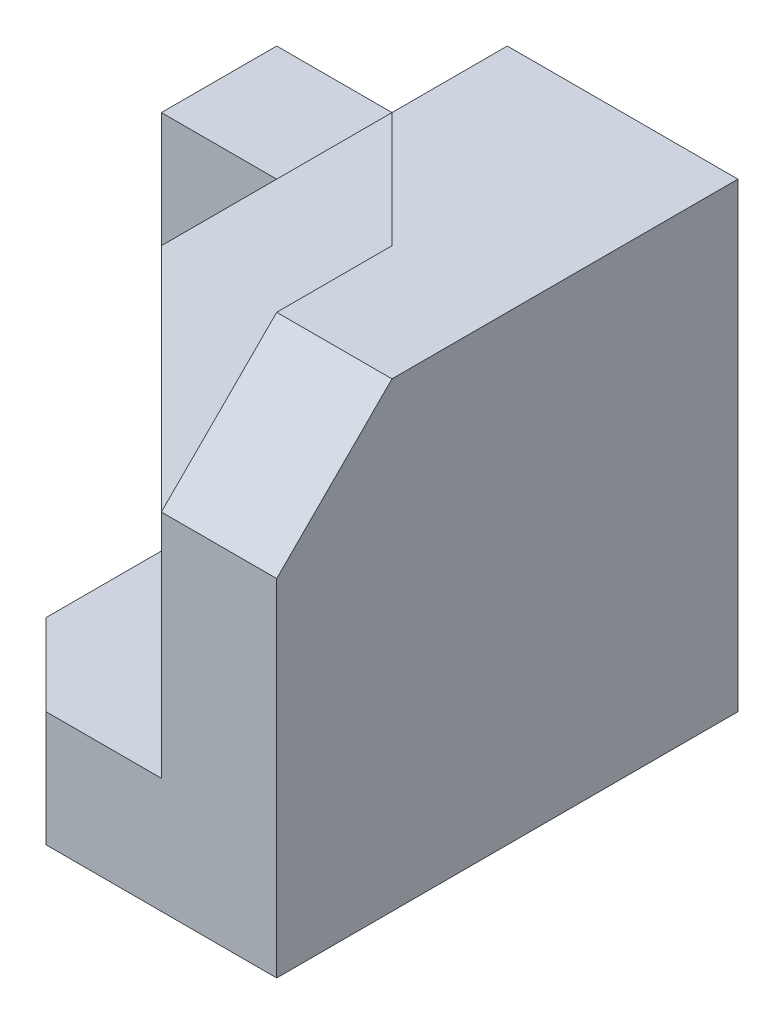
SolidWorks part; units mm, degrees
ref_plane "Front Plane" through (0, 0, 0) normal (0, 0, 1) x (1, 0, 0)
ref_plane "Top Plane" through (0, 0, 0) normal (0, 1, 0) x (1, 0, 0)
ref_plane "Right Plane" through (0, 0, 0) normal (1, 0, 0) x (0, 0, -1)
sketch "Sketch2" plane through (0, 0, 0) normal (0, 1, 0) x (1, 0, 0)
  line L0 (0, 0) -> (10, 0)
  line L1 (10, 0) -> (10, -15)
  line L2 (10, -15) -> (5, -15)
  line L3 (5, -15) -> (5, -10)
  line L4 (5, -10) -> (0, -5)
  line L5 (0, -5) -> (0, 0)
  dimension "D1" = 5
  dimension "D2" = 10
  dimension "D3" = 15
  dimension "D4" = 5
  dimension "D5" = 5
extrude "Boss-Extrude1" add sketch "Sketch2" along normal blind 20
sketch "Sketch3" plane through (0, 0, 15) normal (0, 0, 1) x (1, 0, 0)
  line L1 (5, 0) -> (10, 0)
  line L2 (5, 0) -> (5, 20)
  line L3 (5, 20) -> (10, 20)
  line L4 (10, 0) -> (10, 20)
extrude "Boss-Extrude2" add sketch "Sketch3" along normal blind 5
sketch "Sketch4" plane through (5, 0, 0) normal (-1, 0, 0) x (0, 0, 1)
  line L0 (15, 20) -> (20, 15)
  line L1 (10, 20) -> (20, 20) construction
  line L2 (20, 20) -> (20, 0) construction
  line L3 (20, 15) -> (20, 20)
  line L4 (20, 20) -> (15, 20)
  dimension "D1" = 5
  dimension "D2" = 5
extrude "Cut-Extrude1" cut sketch "Sketch4" against normal blind 5
sketch "Sketch5" plane through (0, 0, 0) normal (-1, 0, 0) x (0, 0, 1)
  line L1 (0, 0) -> (5, 0)
  line L2 (0, 0) -> (0, 20)
  line L3 (0, 20) -> (5, 20)
  line L4 (5, 0) -> (5, 20)
extrude "Boss-Extrude3" add sketch "Sketch5" along normal blind 5
sketch "Sketch6" plane through (0, 0, 5) normal (0, 0, 1) x (1, 0, 0)
  line L0 (0, 20) -> (-5, 20)
  line L1 (-5, 20) -> (-5, 15)
  line L2 (-5, 0) -> (-5, 20) construction
  line L3 (-5, 15) -> (0, 20)
  dimension "D1" = 5
extrude "Cut-Extrude2" cut sketch "Sketch6" against normal blind 5
sketch "Sketch7" plane through (-5, 0, 0) normal (-1, 0, 0) x (0, 0, 1)
  line L1 (0, 0) -> (5, 0)
  line L2 (0, 0) -> (0, 15)
  line L3 (0, 15) -> (5, 15)
  line L4 (5, 0) -> (5, 15)
extrude "Boss-Extrude4" add sketch "Sketch7" along normal blind 5
ref_plane "Plane1" through (0, 0, 0) normal (0, -1, 0) x (-1, 0, 0)
sketch "Sketch8" plane through (0, 0, 0) normal (0, -1, 0) x (-1, 0, 0)
  line L0 (10, -5) -> (0, -5)
  line L1 (0, -5) -> (-5, -10)
  line L2 (-5, -10) -> (-5, -15)
  line L3 (-5, -10) -> (-5, -20) construction
  line L4 (-5, -15) -> (0, -15)
  line L5 (0, -15) -> (10, -5)
  dimension "D1" = 5
  dimension "D2" = 5
extrude "Boss-Extrude6" add sketch "Sketch8" against normal blind 20
sketch3d "3DSketch2"
  line L0 (5, 20, 15) -> (5, 0, 15) construction
  line L1 (0, 20, 15) -> (0, 0, 15) construction
  line L2 (-10, 0, 5) -> (-10, 15, 5) construction
  line L3 (10, 20, 0) -> (0, 20, 0) construction
  line L4 (10, 20, 15) -> (10, 20, 0) construction
  line L5 (5, 20, 15) -> (0, 20, 15) construction
  line L7 (0, 20, 15) -> (-10, 20, 5) construction
  line L8 (0, 20, 5) -> (5, 20, 10)
  line L9 (5, 20, 10) -> (5, 15, 15)
  line L10 (5, 15, 15) -> (0, 10, 15)
  line L11 (0, 10, 15) -> (-10, 10, 5)
  line L12 (-10, 10, 5) -> (0, 20, 5)
  point P0 (0, 20, 5)
  point P1 (5, 20, 10)
  point P3 (5, 15, 15)
  point P4 (0, 10, 15)
  point P7 (-10, 10, 5)
  dimension "D1" = 10
  dimension "D2" = 5
  dimension "D3" = 5
  dimension "D4" = 10
  dimension "D5" = 5
extrude "Cut-Extrude4" cut sketch "3DSketch2" along direction (0, -1, 0) on the side of the normal blind 31
sketch "Sketch9" plane through (0, 0, 0) normal (0, -1, 0) x (-1, 0, 0)
  line L0 (0, -15) -> (-5, -15)
  line L1 (-5, -15) -> (-5, -20)
  line L2 (-5, -20) -> (0, -20)
  line L3 (0, -20) -> (3.5355, -16.4645)
  line L4 (3.5355, -16.4645) -> (3.5355, -11.4645)
  line L5 (0, -15) -> (10, -5) construction
  line L6 (3.5355, -11.4645) -> (0, -15)
  dimension "D1" = 5
  dimension "D2" = 5
extrude "Boss-Extrude7" add sketch "Sketch9" against normal blind 5
